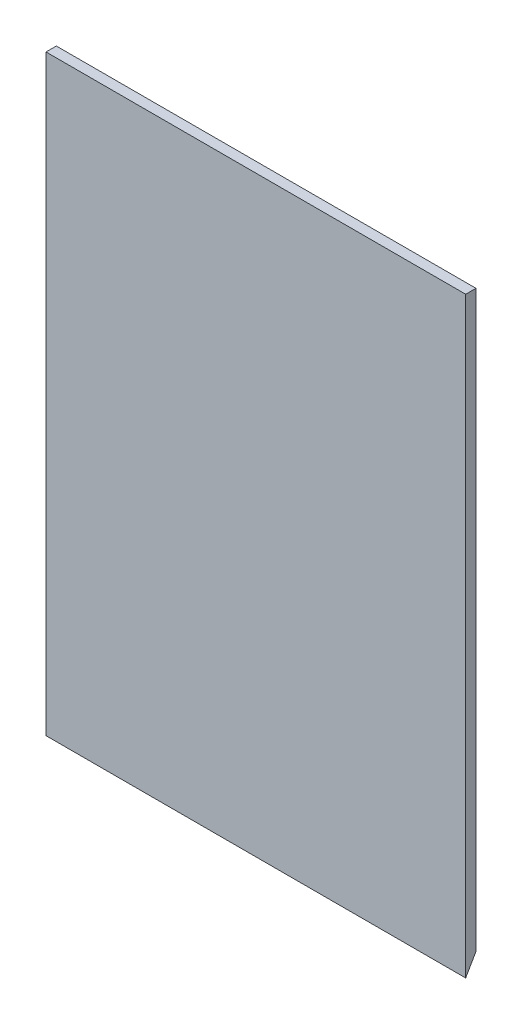
SolidWorks part; units mm, degrees
ref_plane "Front Plane" through (0, 0, 0) normal (0, 0, 1) x (1, 0, 0)
ref_plane "Top Plane" through (0, 0, 0) normal (0, 1, 0) x (1, 0, 0)
ref_plane "Right Plane" through (0, 0, 0) normal (1, 0, 0) x (0, 0, -1)
sketch "Sketch1" plane through (0, 0, 0) normal (0, 0, 1) x (1, 0, 0)
  line L1 (-103.505, 146.05) -> (103.505, 146.05)
  line L2 (-103.505, 146.05) -> (-103.505, -146.05)
  line L3 (-103.505, -146.05) -> (103.505, -146.05)
  line L4 (103.505, 146.05) -> (103.505, -146.05)
  line L5 (-103.505, 146.05) -> (103.505, -146.05) construction
  line L6 (-103.505, -146.05) -> (103.505, 146.05) construction
  point P0 (0, 0)
  dimension "D1" = 207.01
  dimension "D2" = 292.1
extrude "Boss-Extrude1" add sketch "Sketch1" along normal mid plane 5.08
sketch "Sketch4" plane through (-103.505, 0, 0) normal (-1, 0, 0) x (0, 0, 1)
  line L0 (-2.54, -137.2512) -> (2.54, -146.05)
  line L1 (-2.54, 146.05) -> (-2.54, -146.05) construction
  line L2 (2.54, -146.05) -> (-2.54, -146.05)
  line L3 (-2.54, -146.05) -> (-2.54, -137.2512)
  dimension "D1" = 60
extrude "Cut-Extrude3" cut sketch "Sketch4" against normal blind 6.35
sketch "Sketch5" plane through (103.505, 0, 0) normal (1, 0, 0) x (0, 0, -1)
  line L0 (2.54, -137.2512) -> (-2.54, -146.05)
  line L1 (2.54, -146.05) -> (2.54, 146.05) construction
  line L2 (-2.54, -146.05) -> (2.54, -146.05)
  line L3 (2.54, -146.05) -> (2.54, -137.2512)
  dimension "D1" = 60
extrude "Cut-Extrude4" cut sketch "Sketch5" against normal blind 6.35
